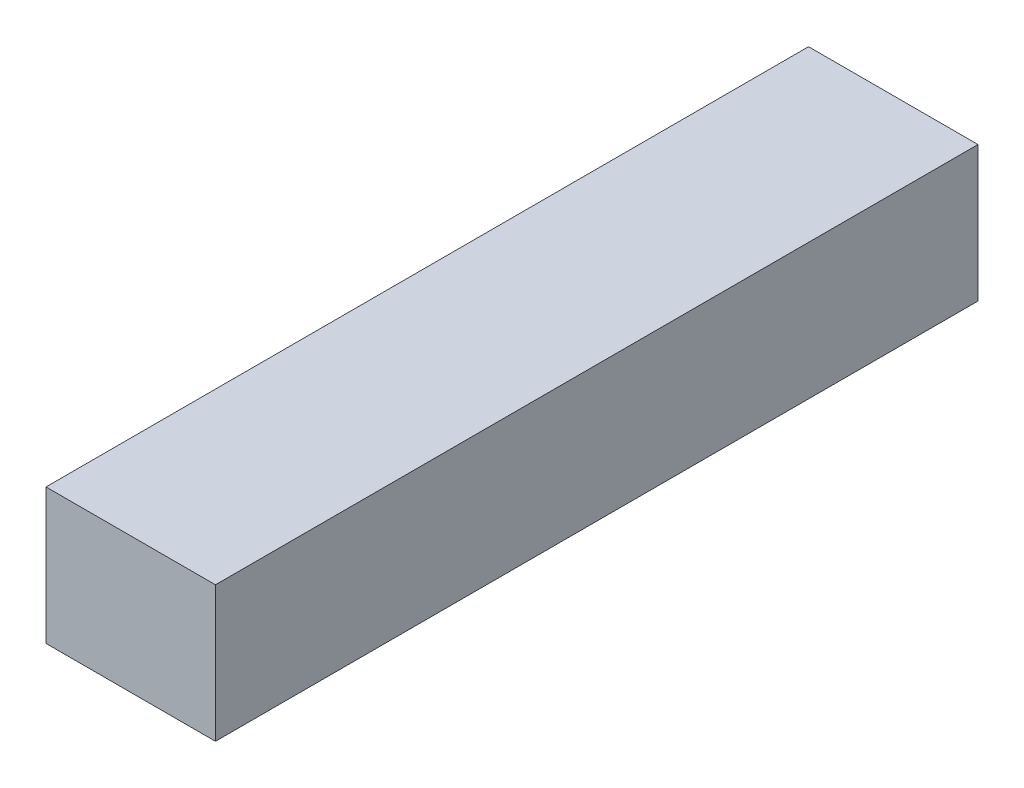
SolidWorks part; units mm, degrees
ref_plane "Front Plane" through (0, 0, 0) normal (0, 0, 1) x (1, 0, 0)
ref_plane "Top Plane" through (0, 0, 0) normal (0, 1, 0) x (1, 0, 0)
ref_plane "Right Plane" through (0, 0, 0) normal (1, 0, 0) x (0, 0, -1)
sketch "Sketch1" plane through (0, 0, 0) normal (0, 0, 1) x (1, 0, 0)
  line L1 (0, 0) -> (10, 0)
  line L2 (0, 0) -> (0, -8)
  line L3 (0, -8) -> (10, -8)
  line L4 (10, 0) -> (10, -8)
extrude "Boss-Extrude1" add sketch "Sketch1" against normal blind 45
